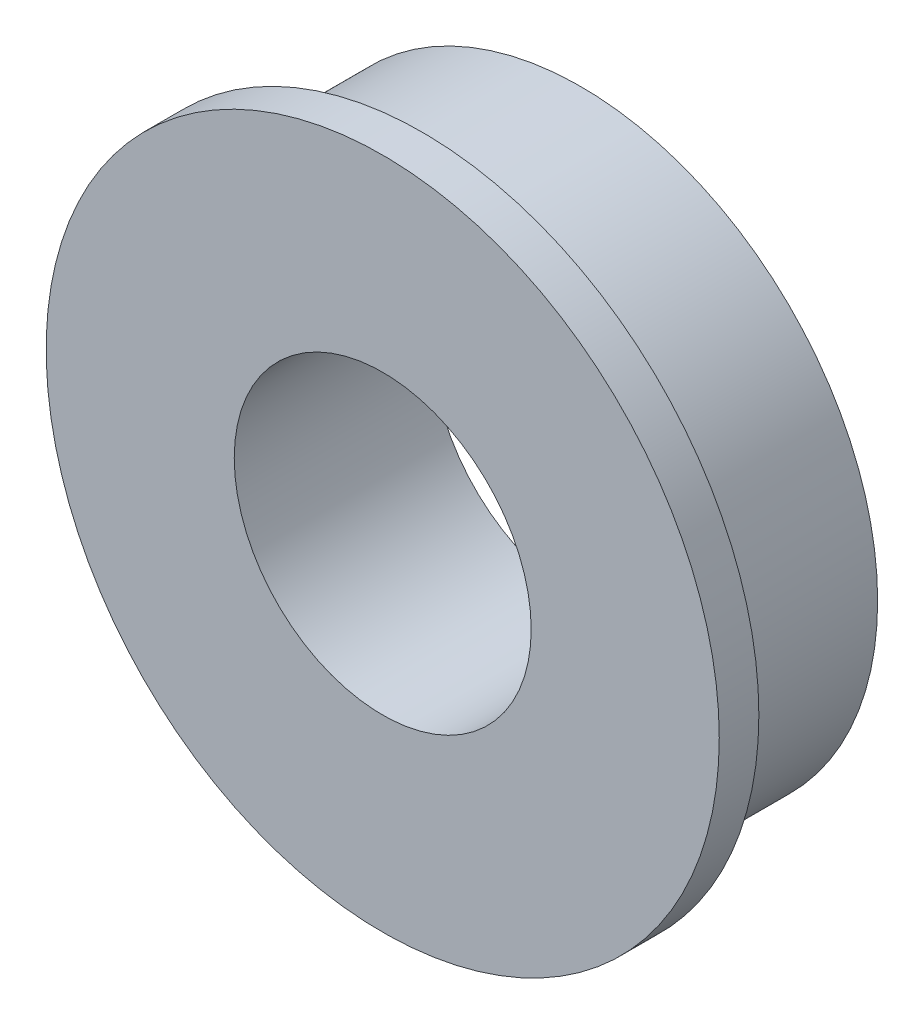
SolidWorks part; units mm, degrees
ref_plane "前视基准面" through (0, 0, 0) normal (0, 0, 1) x (1, 0, 0)
ref_plane "上视基准面" through (0, 0, 0) normal (0, 1, 0) x (1, 0, 0)
ref_plane "右视基准面" through (0, 0, 0) normal (1, 0, 0) x (0, 0, -1)
sketch "草图1" plane through (0, 0, 0) normal (0, 0, 1) x (1, 0, 0)
  circle A0 centre (0, 0) radius 3
  circle A1 centre (0, 0) radius 6
  dimension "D1" = 6
  dimension "D2" = 12
extrude "凸台-拉伸1" add sketch "草图1" along normal blind 3.2
sketch "草图2" plane through (0, 0, 3.2) normal (0, 0, 1) x (1, 0, 0)
  circle A0 centre (0, 0) radius 6.8
  dimension "D1" = 13.6
extrude "凸台-拉伸2" add sketch "草图2" along normal blind 0.8
sketch "草图3" plane through (0, 0, 3.2) normal (0, 0, -1) x (-1, 0, 0)
  circle A0 centre (0, 0) radius 3
  dimension "D1" = 6
extrude "切除-拉伸1" cut sketch "草图3" against normal up to surface (0.8 mm away) up to face at (6.8, 0, 4)
